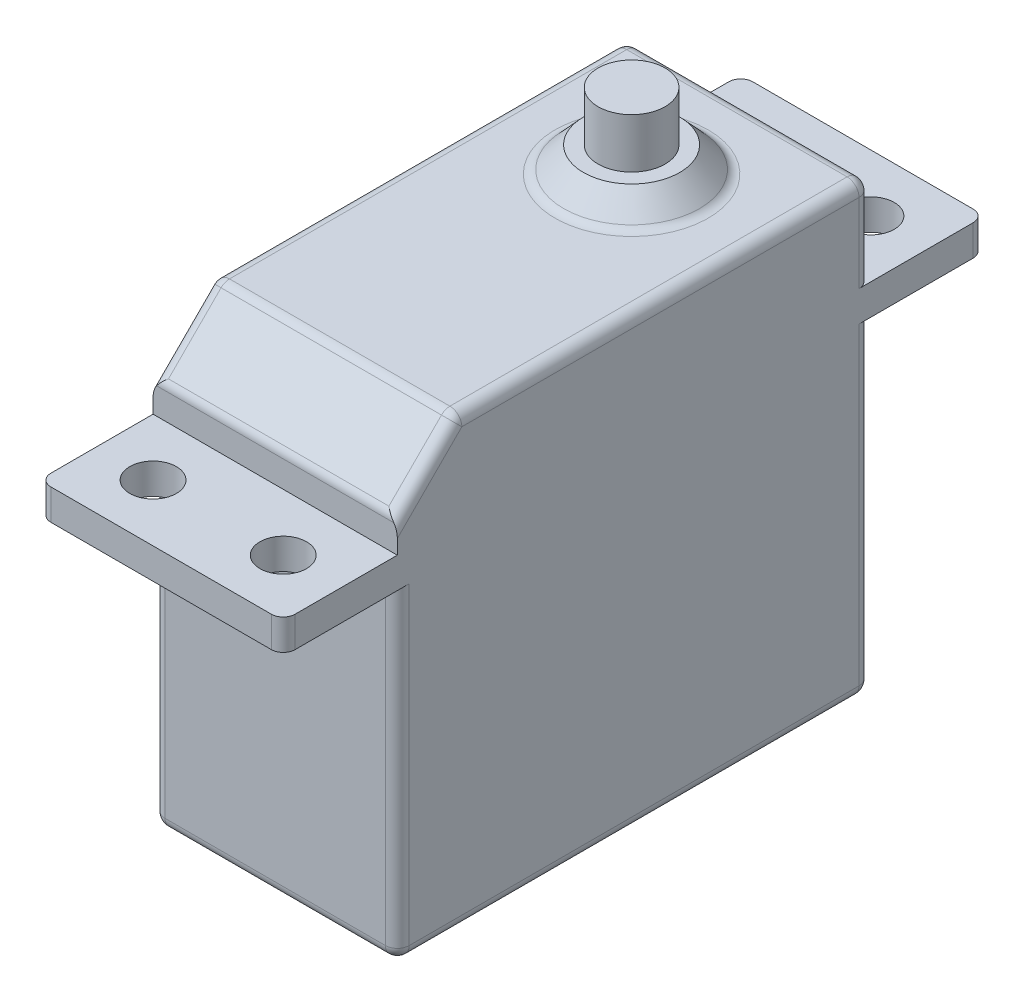
SolidWorks part; units mm, degrees
ref_plane "Front Plane" through (0, 0, 0) normal (0, 0, 1) x (1, 0, 0)
ref_plane "Top Plane" through (0, 0, 0) normal (0, 1, 0) x (1, 0, 0)
ref_plane "Right Plane" through (0, 0, 0) normal (1, 0, 0) x (0, 0, -1)
sketch "Sketch1" plane through (0, 0, 0) normal (0, 1, 0) x (1, 0, 0)
  line L1 (0, 0) -> (20.828, 0)
  line L2 (0, 0) -> (0, 40.386)
  line L3 (0, 40.386) -> (20.828, 40.386)
  line L4 (20.828, 0) -> (20.828, 40.386)
  dimension "D1" = 20.828
  dimension "D2" = 40.386
extrude "Boss-Extrude1" add sketch "Sketch1" along normal blind 38.1
ref_plane "Plane1" through (0, 27.7368, 0) normal (0, 1, 0) x (1, 0, 0)
sketch "Sketch2" plane through (0, 27.7368, 0) normal (0, 1, 0) x (1, 0, 0)
  line L0 (0, 40.386) -> (20.828, 0) construction
  line L1 (0, 40.386) -> (0, 0) construction
  line L2 (20.828, 50.1142) -> (0, 50.1142)
  line L3 (20.828, 50.1142) -> (20.828, -9.7282)
  line L4 (20.828, -9.7282) -> (0, -9.7282)
  line L5 (0, 50.1142) -> (0, -9.7282)
  line L6 (20.828, 50.1142) -> (0, -9.7282) construction
  line L7 (20.828, -9.7282) -> (0, 50.1142) construction
  line L9 (10.414, 19.939) -> (10.414, 50019.939) construction
  line L10 (10.2743, 20.193) -> (50010.2743, 20.193) construction
  line L11 (20.828, 40.386) -> (0, 40.386) construction
  circle A0 centre (4.8641, 45.2501) radius 1.9875
  circle A1 centre (15.9639, 45.2501) radius 1.9876
  circle A2 centre (15.9639, -4.8641) radius 1.9876
  circle A3 centre (4.8641, -4.8641) radius 1.9875
  point P2 (10.414, 20.193)
  dimension "D4" = 3.9751
  dimension "D1" = 4.8641
  dimension "D2" = 4.8641
  dimension "D3" = 4.8641
extrude "Boss-Extrude2" add sketch "Sketch2" along normal blind 2.6162
ref_plane "Plane2" through (10.414, 0, 0) normal (1, 0, 0) x (0, 0, -1)
sketch "Sketch4" plane through (10.414, 0, 0) normal (1, 0, 0) x (0, 0, -1)
  line L0 (40.386, 38.1) -> (40.386, 30.353) construction
  line L1 (40.386, 38.1) -> (0, 38.1) construction
  line L2 (30.3911, 40.259) -> (26.289, 40.259)
  line L3 (26.289, 40.259) -> (24.3078, 38.1)
  line L4 (24.3078, 38.1) -> (30.3911, 38.1)
  line L5 (30.3911, 40.259) -> (30.3911, 38.1)
  dimension "D1" = 2.159
  dimension "D2" = 6.0833
  dimension "D3" = 9.9949
  dimension "D4" = 4.1021
revolve "Revolve1" add sketch "Sketch4" angle 360 about L5
sketch "Sketch5" plane through (0, 40.259, 0) normal (0, 1, 0) x (1, 0, 0)
  circle A0 centre (10.414, 30.3911) radius 2.8575
  dimension "D1" = 5.715
extrude "Boss-Extrude3" add sketch "Sketch5" along normal blind 4.2418
chamfer "Chamfer1" distance 5.08 angle 45 1 edges at (10.414, 38.1, 0)
fillet "Fillet4" radius 1.016 22 edges at (10.414, 38.1, -40.386) (20.828, 38.1, -22.733) (0, 38.1, -22.733) (10.414, 38.1, -24.3078) (10.414, 38.1, -5.08) (20.828, 35.56, -2.54) (10.414, 33.02, 0) (0, 35.56, -2.54) (10.414, 0, -40.386) (0, 13.8684, -40.386) (0, 0, -20.193) (20.828, 0, -20.193) (10.414, 0, 0) (20.828, 13.8684, -40.386) (0, 13.8684, 0) (20.828, 13.8684, 0) (0, 34.2265, -40.386) (20.828, 34.2265, -40.386) (0, 29.0449, 9.7282) (20.828, 29.0449, 9.7282) (0, 29.0449, -50.1142) (20.828, 29.0449, -50.1142)
equation "\"servo width\"= 0.82"
equation "\"servo length\"= 1.59"
equation "\"D1@Sketch1\"=\"servo width\""
equation "\"D2@Sketch1\"=\"servo length\""
equation "\"servo center offset\"= 0.3915"
equation "\"servo hole spacing\"= 0.628"
equation "\"servo hole diameter\"= 0.0905"
equation "\"servo mount diameter\"= 0.1565"
equation "\"servo mount side offset\"= 0.1915"
equation "\"servo mount top offset\"= 0.1915"
equation "\"servo planar offset\"= 0.74"
equation "\"pan bottom length\"= 4"
equation "\"pan arm length\"= 5"
equation "\"tilt bottom length\"= \"border\" + \"servo hole spacing\" + \"camera height\" + \"plywood thickness\" + \"servo planar offset\""
equation "\"tilt arm length\"= \"pan bottom length\" - \"border\" + \"servo hole spacing\" - \"servo planar offset\" -  \"plywood thickness\" + \"servo hole diameter\"/2"
equation "\"arm width\"= 1.5"
equation "\"plywood thickness\"= 0.19"
equation "\"camera backset\"= 0.8"
equation "\"camera height\"= 0.89"
equation "\"center rod diameter\"= 0.25"
equation "\"D1@Sketch2\"=\"servo mount top offset\""
equation "\"D2@Sketch2\"=\"servo mount side offset\""
equation "\"D4@Sketch2\"=\"servo mount diameter\""
equation "\"D3@Sketch2\"=\"servo mount top offset\""
equation "\"leg diameter\"= 0.45"
equation "\"leg length\"= 1.5"
equation "\"border\"= 0.5"
equation "\"crossbrace small length\"= 1"
equation "\"crossbrace small width\"= 1"
equation "\"crossbrace large length\"= 1"
equation "\"crossbrace large width\"= 1"
